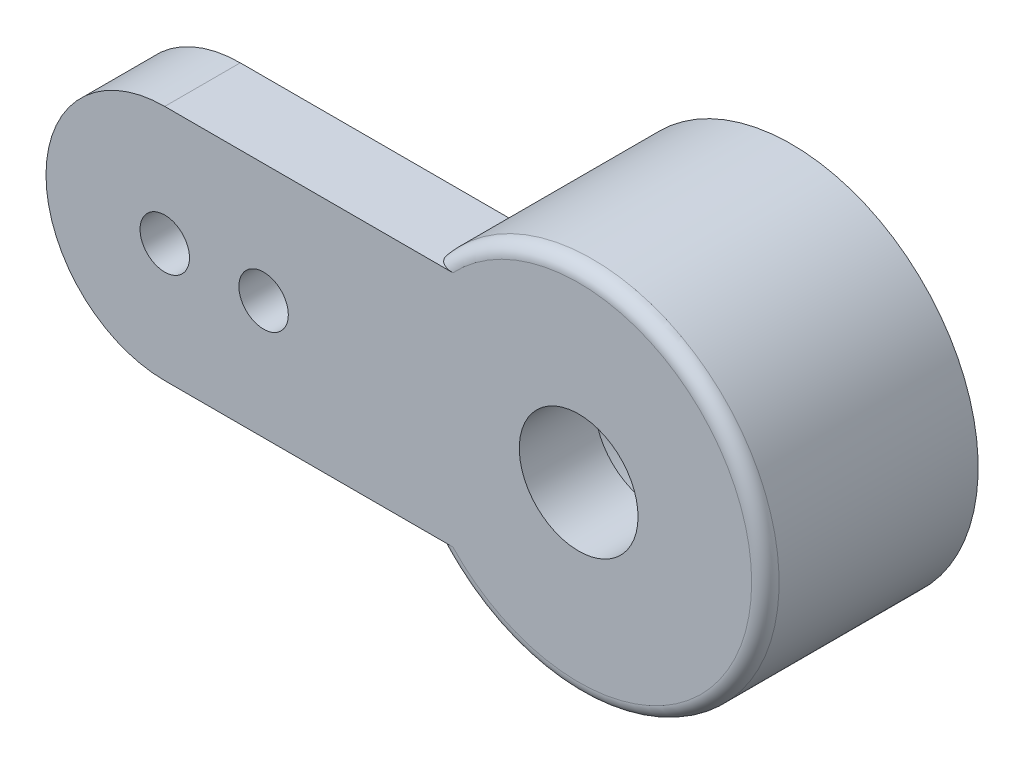
SolidWorks part; units mm, degrees
ref_plane "前视基准面" through (0, 0, 0) normal (0, 0, 1) x (1, 0, 0)
ref_plane "上视基准面" through (0, 0, 0) normal (0, 1, 0) x (1, 0, 0)
ref_plane "右视基准面" through (0, 0, 0) normal (1, 0, 0) x (0, 0, -1)
other "Configuration Table"
sketch "草图1" plane through (0, 0, 0) normal (0, 0, 1) x (1, 0, 0)
  line L0 (-6.03, 0) -> (0, 0) construction
  line L1 (-6.03, 1.73) -> (0, 1.73)
  line L2 (-6.03, -1.73) -> (0, -1.73)
  line L3 (-7.76, 6.9336) -> (-7.76, -7.6791) construction
  line L4 (2.72, 6.9336) -> (2.72, -9.1063) construction
  circle A0 centre (0, 0) radius 2.72
  arc A1 (-6.03, 1.73) -> (-6.03, -1.73) centre (-6.03, 0) ccw
  arc A2 (0, -1.73) -> (0, 1.73) centre (0, 0) ccw
  circle A3 centre (0, 0) radius 0.865
  circle A4 centre (-6.03, 0) radius 0.36
  circle A5 centre (-4.59, 0) radius 0.36
  point P4 (-3.015, 0)
  dimension "D1" = 5.44
  dimension "D4" = 1.73
  dimension "D5" = 0.72
  dimension "D2" = 10.48
  dimension "D3" = 3.46
  dimension "D6" = 1.44
extrude "凸台-拉伸1" add sketch "草图1" along normal blind 1.1 contours L1 A1 L2 A0 A5 A4 | L2 A2 L1 A0 A3 | A2 L2 A0 L1
sketch "草图2" plane through (0, 0, 0) normal (0, 0, -1) x (-1, 0, 0)
  arc A0 (2.0989, 1.73) -> (2.0989, -1.73) centre (0, 0) ccw construction
  circle A1 centre (0, 0) radius 1.95
  circle A2 centre (0, 0) radius 2.72
  dimension "D1" = 3.9
extrude "凸台-拉伸2" add sketch "草图2" along normal blind 2
fillet "圆角1" radius 0.2 1 edges at (2.72, 0, 1.1)
